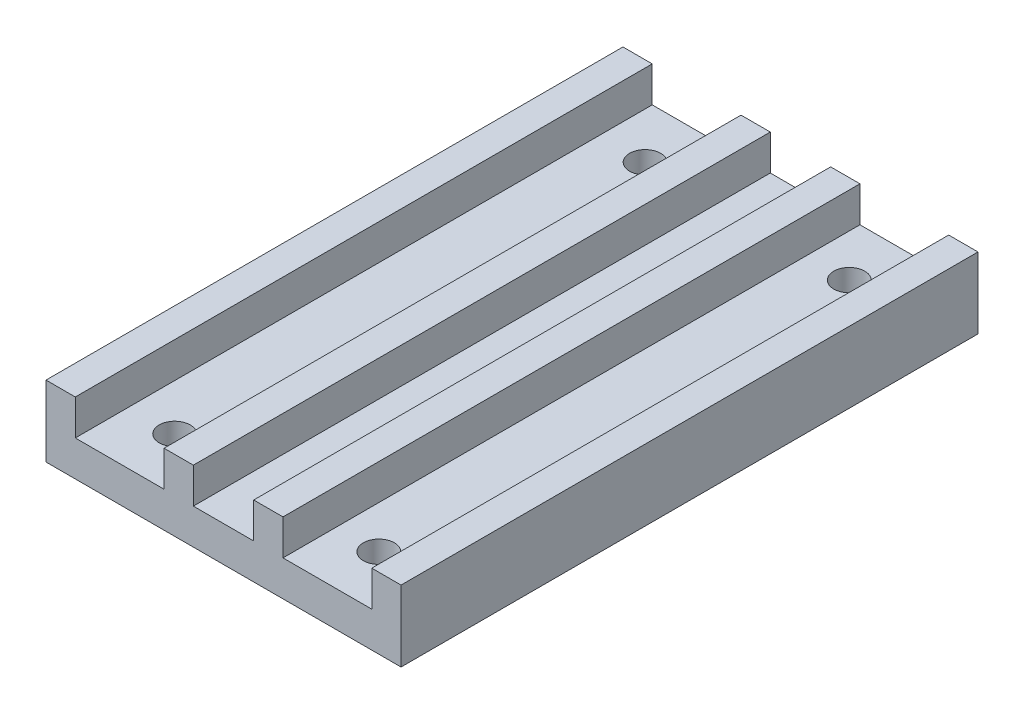
SolidWorks part; units mm, degrees
ref_plane "Front Plane" through (0, 0, 0) normal (0, 0, 1) x (1, 0, 0)
ref_plane "Top Plane" through (0, 0, 0) normal (0, 1, 0) x (1, 0, 0)
ref_plane "Right Plane" through (0, 0, 0) normal (1, 0, 0) x (0, 0, -1)
sketch "Sketch1" plane through (0, 0, 0) normal (0, 1, 0) x (1, 0, 0)
  line L0 (-20, -20) -> (20, -20) construction
  line L1 (-20, -32.5) -> (20, -32.5)
  line L2 (-20, -32.5) -> (-20, 32.5)
  line L3 (-20, 32.5) -> (20, 32.5)
  line L4 (20, -32.5) -> (20, 32.5)
  line L5 (-20, -32.5) -> (20, 32.5) construction
  line L6 (-20, 32.5) -> (20, -32.5) construction
  line L7 (0, 0) -> (0, -32.5) construction
  line L8 (0, 0) -> (20, 0) construction
  circle A0 centre (11.5, -26.5) radius 1.75
  circle A1 centre (-11.5, -26.5) radius 1.75
  circle A2 centre (11.5, 26.5) radius 1.75
  circle A3 centre (-11.5, 26.5) radius 1.75
  point P0 (0, 0)
  dimension "D4" = 6.5
  dimension "D5" = 3.5
  dimension "D1" = 40
  dimension "D2" = 65
  dimension "D3" = 20
  dimension "D6" = 11.5
extrude "Boss-Extrude1" add sketch "Sketch1" along normal blind 4
sketch "Sketch2" plane through (0, 4, 0) normal (0, 1, 0) x (1, 0, 0)
  line L0 (-20, -32.5) -> (20, -32.5) construction
  line L1 (-20, 32.5) -> (-16.7, 32.5)
  line L2 (-20, 32.5) -> (-20, -32.5)
  line L3 (-20, -32.5) -> (-16.7, -32.5)
  line L4 (-16.7, 32.5) -> (-16.7, -32.5)
  line L5 (20, 32.5) -> (-20, 32.5) construction
  line L6 (20, 32.5) -> (16.7, 32.5)
  line L7 (20, 32.5) -> (20, -32.5)
  line L8 (20, -32.5) -> (16.7, -32.5)
  line L9 (16.7, 32.5) -> (16.7, -32.5)
  line L10 (-6.7, 32.5) -> (-3.4, 32.5)
  line L11 (-6.7, 32.5) -> (-6.7, -32.5)
  line L12 (-6.7, -32.5) -> (-3.4, -32.5)
  line L13 (-3.4, 32.5) -> (-3.4, -32.5)
  line L15 (3.4, 32.5) -> (6.7, 32.5)
  line L16 (3.4, 32.5) -> (3.4, -32.5)
  line L17 (3.4, -32.5) -> (6.7, -32.5)
  line L18 (6.7, 32.5) -> (6.7, -32.5)
  dimension "D1" = 3.3
  dimension "D2" = 10
  dimension "D3" = 3.3
  dimension "D4" = 3.3
  dimension "D5" = 3.3
  dimension "D6" = 10
extrude "Boss-Extrude2" add sketch "Sketch2" along normal blind 4
